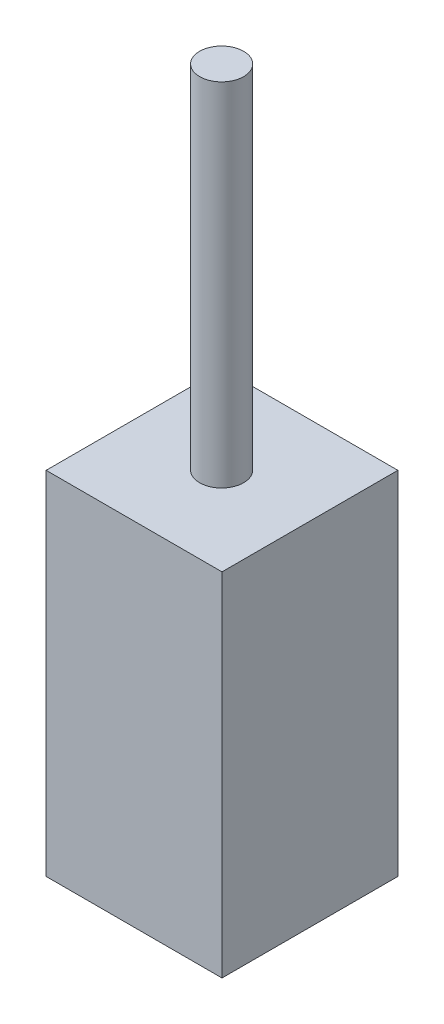
SolidWorks part; units mm, degrees
material "ASTM A36 Steel"
ref_plane "Front Plane" through (0, 0, 0) normal (0, 0, 1) x (1, 0, 0)
ref_plane "Top Plane" through (0, 0, 0) normal (0, 1, 0) x (1, 0, 0)
ref_plane "Right Plane" through (0, 0, 0) normal (1, 0, 0) x (0, 0, -1)
sketch "Sketch1" plane through (0, 0, 0) normal (0, 1, 0) x (1, 0, 0)
  line L1 (0, 0) -> (25.4, 0)
  line L2 (0, 0) -> (0, 25.4)
  line L3 (0, 25.4) -> (25.4, 25.4)
  line L4 (25.4, 0) -> (25.4, 25.4)
  dimension "D1" = 25.4
  dimension "D2" = 25.4
extrude "Boss-Extrude1" add sketch "Sketch1" along normal blind 50.8
sketch "Sketch2" plane through (0, 50.8, 0) normal (0, 1, 0) x (1, 0, 0)
  line L0 (25.4, 25.4) -> (0, 25.4) construction
  line L2 (0, 25.4) -> (0, 0) construction
  circle A0 centre (12.6481, 12.7) radius 3.175
  dimension "D3" = 6.35
  dimension "D1" = 12.7
  dimension "D2" = 12.6481
extrude "Boss-Extrude2" add sketch "Sketch2" along normal blind 50.8
sketch "Sketch3" plane through (0, 0, 0) normal (-1, 0, 0) x (0, 0, 1)
  text T0 "MEOW"
extrude "Cut-Extrude1" cut sketch "Sketch3" against normal blind 1.27
